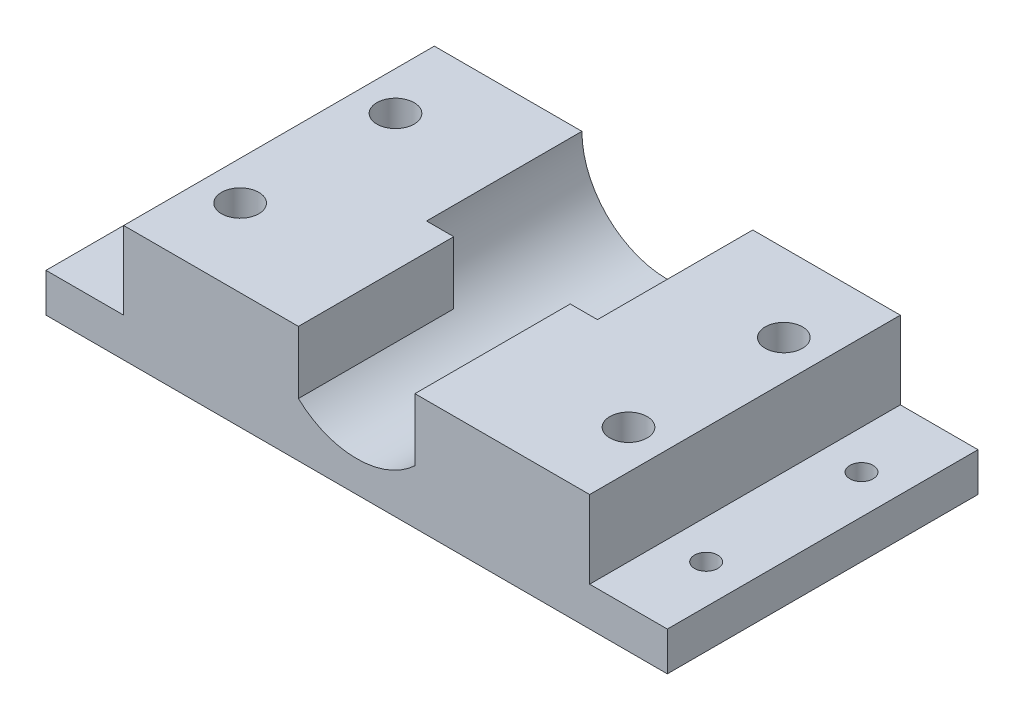
SolidWorks part; units mm, degrees
ref_plane "Plan de face" through (0, 0, 0) normal (0, 0, 1) x (1, 0, 0)
ref_plane "Plan de dessus" through (0, 0, 0) normal (0, 1, 0) x (1, 0, 0)
ref_plane "Plan de droite" through (0, 0, 0) normal (1, 0, 0) x (0, 0, -1)
sketch "Esquisse1" plane through (0, 0, 0) normal (0, 0, 1) x (1, 0, 0)
  line L0 (60, 15) -> (60, 5)
  line L1 (0, 0) -> (60, 0)
  line L3 (0, 15) -> (60, 15)
  line L5 (60, 5) -> (70, 5)
  line L7 (60, 0) -> (70, 0)
  line L8 (70, 5) -> (70, 0)
  line L9 (0, 0) -> (-10, 0)
  line L11 (0, 5) -> (-10, 5)
  line L12 (-10, 0) -> (-10, 5)
  line L13 (0, 15) -> (0, 5)
  dimension "D1" = 60
  dimension "D2" = 15
  dimension "D3" = 10
  dimension "D4" = 10
  dimension "D5" = 5
  dimension "D6" = 5
extrude "base_mors" add sketch "Esquisse1" along normal blind 40
sketch "Esquisse2" plane through (0, 0, 40) normal (0, 0, 1) x (1, 0, 0)
  line L0 (60, 15) -> (0, 15) construction
  circle A0 centre (30, 15) radius 11
extrude "emplacement_moteur" cut sketch "Esquisse2" against normal through all
sketch "Esquisse3" plane through (0, 5, 0) normal (0, 1, 0) x (1, 0, 0)
  line L0 (0, 0) -> (-10, 0) construction
  line L1 (-10, -40) -> (-10, 0) construction
  line L2 (70, 0) -> (60, 0) construction
  line L3 (70, -40) -> (70, 0) construction
  line L4 (0, -40) -> (-10, -40) construction
  line L5 (70, -40) -> (60, -40) construction
  circle A0 centre (-5, -10) radius 1.5
  circle A1 centre (65, -10) radius 1.5
  circle A2 centre (65, -30) radius 1.5
  circle A3 centre (-5, -30) radius 1.5
  dimension "D1" = 10
  dimension "D5" = 5
  dimension "D2" = 5
  dimension "D3" = 10
  dimension "D4" = 5
  dimension "D6" = 5
  dimension "D7" = 10
  dimension "D8" = 10
extrude "trou_fixations_base" cut sketch "Esquisse3" against normal through all
sketch "Esquisse4" plane through (0, 15, 0) normal (0, 1, 0) x (1, 0, 0)
  line L0 (19, 0) -> (0, 0) construction
  line L1 (0, -40) -> (0, 0) construction
  line L2 (60, 0) -> (41, 0) construction
  line L3 (60, -40) -> (60, 0) construction
  line L4 (19, -40) -> (0, -40) construction
  line L5 (60, -40) -> (41, -40) construction
  line L6 (0, -40) -> (0, 0) construction
  circle A0 centre (5, -10) radius 2.4
  circle A1 centre (55, -10) radius 2.4
  circle A2 centre (55, -30) radius 2.4
  circle A4 centre (5, -30) radius 2.4
  dimension "D1" = 10
  dimension "D5" = 10
  dimension "D2" = 5
  dimension "D3" = 10
  dimension "D4" = 5
  dimension "D6" = 10
  dimension "D7" = 5
  dimension "D8" = 5
extrude "trou_fixation_mors_superieur" cut sketch "Esquisse4" against normal blind 6
sketch "Esquisse6" plane through (0, 0, 40) normal (0, 0, 1) x (1, 0, 0)
  line L1 (19, 15) -> (22.5, 15)
  line L2 (19, 15) -> (19, 3)
  line L3 (19, 3) -> (22.5, 3)
  line L4 (22.5, 15) -> (22.5, 3)
  line L5 (41, 15) -> (37.5, 15)
  line L6 (41, 15) -> (41, 3)
  line L7 (41, 3) -> (37.5, 3)
  line L8 (37.5, 15) -> (37.5, 3)
  dimension "D1" = 12
  dimension "D2" = 12
  dimension "D3" = 3.5
  dimension "D4" = 3.5
extrude "encoche moteur" add sketch "Esquisse6" against normal blind 20
